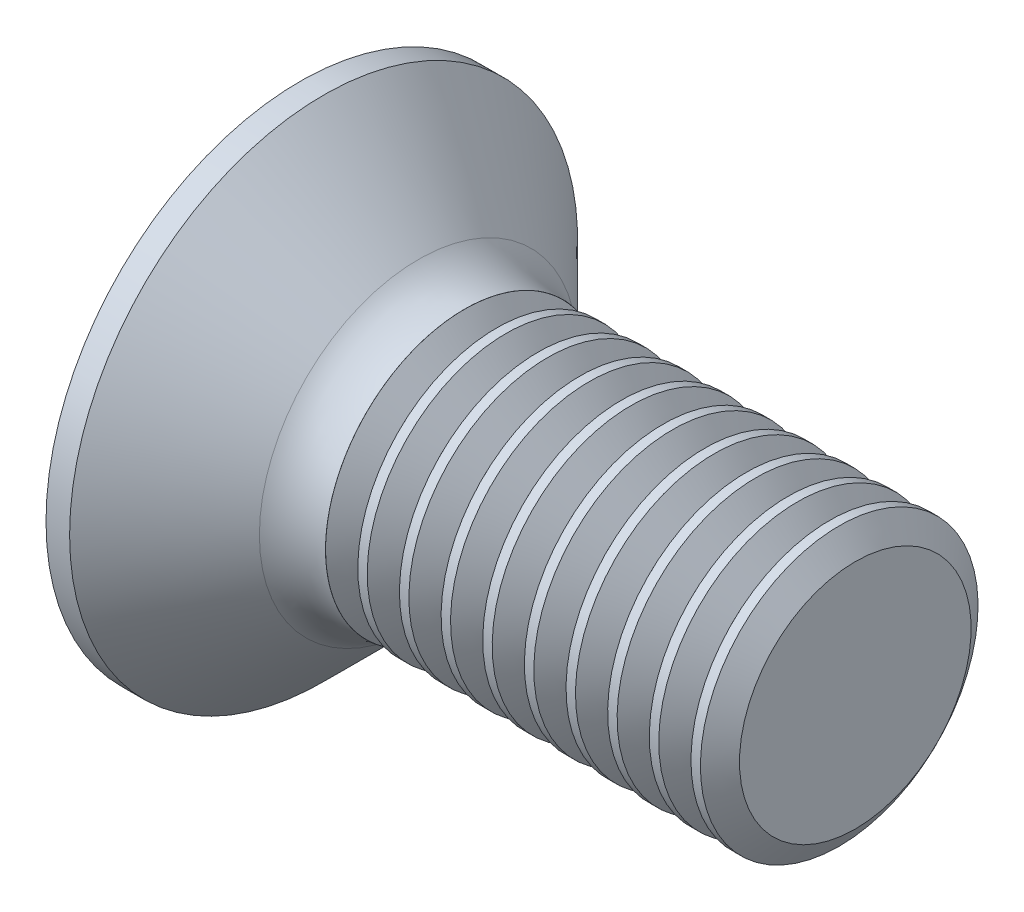
SolidWorks part; units mm, degrees
ref_plane "Plane1" through (0, 0, 0) normal (0, 0, 1) x (1, 0, 0)
ref_plane "Plane2" through (0, 0, 0) normal (0, 1, 0) x (1, 0, 0)
ref_plane "Plane3" through (0, 0, 0) normal (1, 0, 0) x (0, 0, -1)
revolve "Base-Revolve" add sketch "BodySke" angle 360 about L5
sketch "BodySke" plane through (0, 0, 0) normal (0, 0, 1) x (1, 0, 0)
  line L0 (0, 0) -> (0, 9.15)
  line L1 (0, 9.15) -> (0.85, 9.15)
  line L2 (5, 5) -> (20, 5)
  line L3 (20, 5) -> (20, 0)
  line L4 (20, 0) -> (0, 0)
  line L5 (-6.35, 0) -> (82.55, 0) construction
  line L6 (5, -5) -> (20, -5) construction
  line L7 (0.85, -9.15) -> (5, -5) construction
  line L8 (0.85, 9.15) -> (5, 5)
  line L9 (0, -9.15) -> (0.85, -9.15) construction
  line L10 (6.5, 6.5875) -> (6.5, -2.9375) construction
  line L11 (0, 6.35) -> (0, -3.175) construction
  dimension "Diameter" = 10
  dimension "Length" = 20
  dimension "Head_ht" = 5
  dimension "Head_dia" = 18.3
  dimension "Head_ang" = 90
  dimension "D6" = 0.85
  dimension "Advance" = 1.5
  dimension "Thread_nom" = 20
cosmetic thread "ThreadCosmetic" [suppressed] parameters "Thread_length"=13.5, "Thread_minor"=8.344
fillet "Fillet1" radius 2.5 1 edges at (5, 0, 5)
sketch "Sketch3" plane through (0, 0, 0) normal (-1, 0, 0) x (0, 0, 1)
  line L0 (-1.08, 4.9) -> (1.08, 4.9)
  line L1 (1.08, 4.9) -> (1.08, -4.9)
  line L2 (1.08, -4.9) -> (-1.08, -4.9)
  line L3 (-1.08, -4.9) -> (-1.08, 4.9)
  dimension "D1" = 4.9
  dimension "Cross_dia" = 9.8
  dimension "D2" = 1.08
  dimension "Cross_width" = 2.16
ref_plane "Plane4" through (5.64, 0, 0) normal (-1, 0, 0) x (0, 0, 1)
sketch "Sketch4" plane through (5.64, 0, 0) normal (-1, 0, 0) x (0, 0, 1)
  line L0 (-1.08, 2.088) -> (1.08, 2.088)
  line L3 (1.08, 2.088) -> (1.08, -2.088)
  line L4 (1.08, -2.088) -> (-1.08, -2.088)
  line L5 (-1.08, -2.088) -> (-1.08, 2.088)
  dimension "D1" = 2.16
  dimension "D2" = 4.176
  dimension "D3" = 1.08
  dimension "D4" = 2.088
loft "Recess" cut profiles "Sketch3", "Sketch4"
pattern_circular "RecPat" count 2 every 90 about axis through (0, 0, 0) along (1, 0, 0) of "Recess"
sketch "RecCorSke" plane through (0, 0, 0) normal (0, 0, 1) x (1, 0, 0)
  line L0 (-3.175, 0) -> (15.875, 0) construction
  line L2 (0, 0) -> (0, 2.3249)
  line L3 (0, 2.3249) -> (5.64, 1.9305)
  line L4 (5.64, 1.9305) -> (6.2673, 0)
  line L5 (6.2673, 0) -> (0, 0)
  dimension "Diameter" = 3.861
  dimension "Depth" = 5.64
  dimension "Draft_angle" = 4
  dimension "Bottom_angle" = 18
revolve "RecessCore" cut sketch "RecCorSke" angle 360 about L0
sketch "ThdSchSke" plane through (0, 0, 0) normal (0, 0, 1) x (1, 0, 0)
  line L0 (6.5, -4.172) -> (5.9202, -5)
  line L1 (6.5, -4.172) -> (7.0798, -5)
  line L2 (7.0798, -5) -> (7.0798, -6.25)
  line L3 (-3.175, 0) -> (5.1513, 0) construction
  line L5 (7.0798, -6.25) -> (5.9202, -6.25)
  line L6 (5.9202, -6.25) -> (5.9202, -5)
  line L7 (0, 9.15) -> (0, -9.15) construction
  dimension "Thread_minor" = 8.344
  dimension "Diameter" = 10
  dimension "Start" = 6.5
  dimension "SideAngle" = 55
  dimension "VeeAngle" = 70
  dimension "Overcut" = 12.5
revolve "ThreadSchematic" cut sketch "ThdSchSke" angle 360 about L3
pattern_linear "ThdSchPat" count 10 spacing 1.5 along (1, 0, 0) of "ThreadSchematic"
equation "\"D1@Sketch3\" = \"Cross_dia@Sketch3\" / 2"
equation "\"D2@Sketch3\" = \"Cross_width@Sketch3\" / 2"
equation "\"Depth@RecCorSke\" = \"Cross_depth@Plane4\""
equation "\"D1@Sketch4\" = \"Cross_width@Sketch3\""
equation "\"D2@Sketch4\" = \"Cross_dia@Sketch3\" - 2.0 * \"Cross_depth@Plane4\" * tan(26.5  * 0.017453292)"
equation "\"D3@Sketch4\" = \"D1@Sketch4\" / 2"
equation "\"D4@Sketch4\" = \"D2@Sketch4\" / 2"
equation "\"Thread_length@ThreadCosmetic\" = ((sgn( (\"Length@BodySke\" - \"Advance@BodySke\" * 1.0 - \"Head_ht@BodySke\" ) - \"Thread_nom@BodySke\" )-1)*( (\"Length@BodySke\" - \"Advance@BodySke\" * 1.0 - \"Head_ht@BodySke\" ) - \"Thread_nom@BodySke\" ))/-2+ \"Thread_nom@BodySke\""
equation "\"Thread_minor@ThdSchSke\" = \"Thread_minor@ThreadCosmetic\""
equation "\"Diameter@ThdSchSke\" = \"Diameter@BodySke\""
equation "\"Overcut@ThdSchSke\" = \"Diameter@BodySke\" * 1.25"
equation "\"Start@ThdSchSke\" = 0.000001 + \"Length@BodySke\" - \"Thread_length@ThreadCosmetic\"  '---Countersunk---"
equation "\"Num_threads@ThdSchPat\" = int( \"Thread_length@ThreadCosmetic\" / \"Advance@BodySke\" + 0.999 )  + 1"
equation "\"Advance@ThdSchPat\" = \"Thread_length@ThreadCosmetic\" /  (\"Num_threads@ThdSchPat\" - 1) 'relax it"
